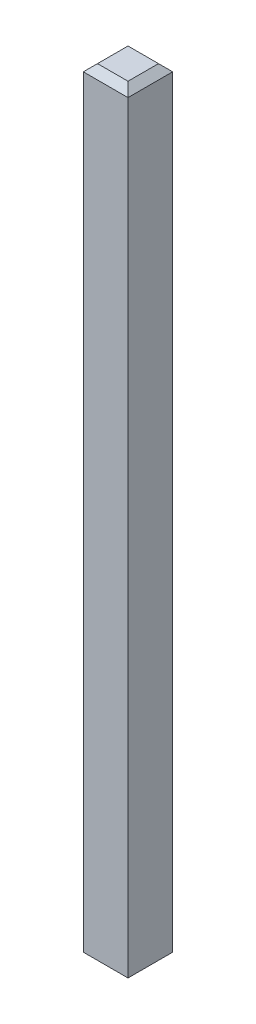
SolidWorks part; units mm, degrees
material "1023 Carbon Steel Sheet (SS)"
ref_plane "Front Plane" through (0, 0, 0) normal (0, 0, 1) x (1, 0, 0)
ref_plane "Top Plane" through (0, 0, 0) normal (0, 1, 0) x (1, 0, 0)
ref_plane "Right Plane" through (0, 0, 0) normal (1, 0, 0) x (0, 0, -1)
sketch "Sketch1" plane through (0, 0, 0) normal (0, 1, 0) x (1, 0, 0)
  line L1 (-0.315, 0.315) -> (0.315, 0.315)
  line L2 (-0.315, 0.315) -> (-0.315, -0.315)
  line L3 (-0.315, -0.315) -> (0.315, -0.315)
  line L4 (0.315, 0.315) -> (0.315, -0.315)
  line L5 (-0.315, 0.315) -> (0.315, -0.315) construction
  line L6 (-0.315, -0.315) -> (0.315, 0.315) construction
  point P0 (0, 0)
  dimension "D1" = 0.63
extrude "Boss-Extrude1" add sketch "Sketch1" along normal blind 10.95
chamfer "Chamfer1" distance 0.1 angle 45 8 edges at (0, 0, -0.315) (-0.315, 0, 0) (0, 0, 0.315) (0.315, 0, 0) (0, 10.95, 0.315) (-0.315, 10.95, 0) (0, 10.95, -0.315) (0.315, 10.95, 0)
equation "\"pin length\"= 10.95"
equation "\"pin width\"= .63"
equation "\"D1@Sketch1\"=\"pin width\""
equation "\"D1@Boss-Extrude1\"=\"pin length\""
